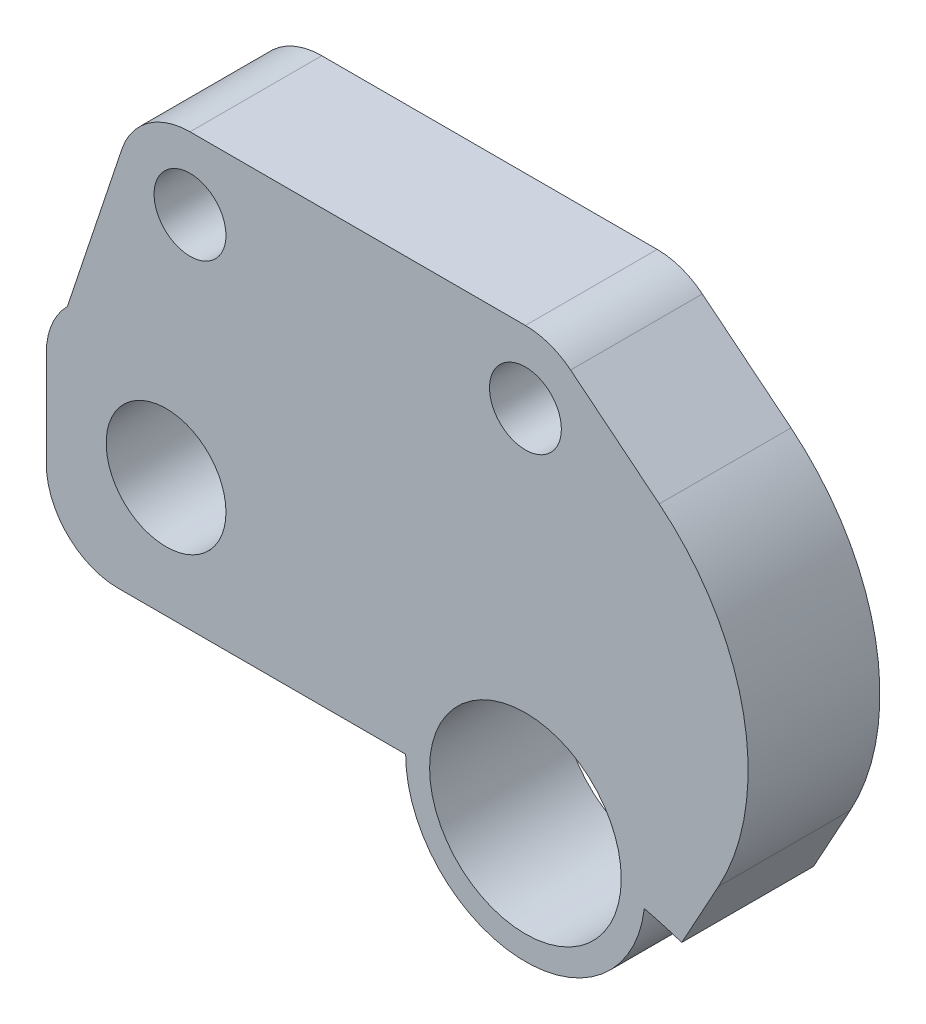
SolidWorks part; units mm, degrees
ref_plane "Alzado" through (0, 0, 0) normal (0, 0, 1) x (1, 0, 0)
ref_plane "Planta" through (0, 0, 0) normal (0, 1, 0) x (1, 0, 0)
ref_plane "Vista lateral" through (0, 0, 0) normal (1, 0, 0) x (0, 0, -1)
sketch "Croquis1" plane through (0, 0, 0) normal (0, 0, 1) x (1, 0, 0)
  line L0 (0, 0) -> (0, -20.95) construction
  line L1 (0, 0) -> (0, 20.95) construction
  line L2 (-20, 25.95) -> (-15, 25.95) construction
  line L3 (0, 20.95) -> (-4, 20.95)
  line L4 (0, 20.95) -> (0, 24.95)
  line L5 (0, 30.95) -> (-17, 30.95)
  line L6 (-20, 23.95) -> (-20, 27.95)
  line L7 (0, -25.95) -> (15.9531, -25.95)
  line L8 (-5, 20.95) -> (-17, 20.95)
  line L9 (0, 0) -> (18.3494, 18.3494) construction
  line L10 (0, 0) -> (25.95, 0) construction
  line L11 (-14, 30.95) -> (-14, 32.95) construction
  line L12 (0, 30.95) -> (0, 35.95) construction
  line L13 (0, 35.95) -> (-14, 35.95) construction
  line L14 (-16.8461, 36.8985) -> (-19.1213, 30.0713)
  line L15 (-14, 38.95) -> (0, 38.95)
  line L16 (1.8868, 38.2824) -> (19.4651, 24.0627)
  line L17 (-14, 34.45) -> (-14, 35.95) construction
  arc A0 (-3.9817, -20.5681) -> (3.9817, -20.5681) centre (0, 0) ccw
  arc A1 (17.6654, -25.4133) -> (0, 30.95) centre (0, 0) ccw
  arc A2 (-5, 20.95) -> (4.9643, 20.3533) centre (0, 20.95) ccw
  arc A3 (4.9643, -20.3533) -> (0, -25.95) centre (0, -20.95) ccw
  circle A4 centre (0, 20.95) radius 4
  circle A5 centre (0, -20.95) radius 4
  circle A6 centre (-15, 25.95) radius 2.5
  circle A7 centre (0, 0) radius 25.95 construction
  arc A8 (4.9643, -20.3533) -> (4.9643, 20.3533) centre (0, 0) ccw
  circle A9 centre (18.3494, 18.3494) radius 2
  circle A10 centre (25.95, 0) radius 2
  arc A11 (15.9531, -25.95) -> (17.6654, -25.4133) centre (15.9531, -22.95) ccw
  arc A12 (-17, 20.95) -> (-20, 23.95) centre (-17, 23.95) cw
  arc A13 (-17, 30.95) -> (-20, 27.95) centre (-17, 27.95) ccw
  circle A14 centre (-14, 35.95) radius 1.5
  circle A15 centre (0, 35.95) radius 1.5
  arc A16 (-14, 38.95) -> (-16.8461, 36.8985) centre (-14, 35.95) ccw
  arc A17 (1.8868, 38.2824) -> (0, 38.95) centre (0, 35.95) ccw
  arc A18 (13.1759, 16.288) -> (19.4651, 24.0627) centre (16.3205, 20.1753) ccw
  point P32 (-20, 30.95)
  dimension "D1" = 41.9
  dimension "D3" = 10
  dimension "D4" = 10
  dimension "D5" = 10
  dimension "D6" = 8
  dimension "D7" = 8
  dimension "D9" = 5
  dimension "D12" = 5
  dimension "D13" = 4
  dimension "D14" = 4
  dimension "D17" = 3
  dimension "D18" = 5
  dimension "D19" = 3
  dimension "D20" = 3
  dimension "D22" = 6
  dimension "D2" = 180
  dimension "D8" = 20
  dimension "D10" = 5
  dimension "D11" = 90
  dimension "D15" = 45
  dimension "D16" = 45
  dimension "D21" = 6
extrude "Saliente-Extruir1" add sketch "Croquis1" along normal blind 5.5 contours A8 A3 L7 A1 L5 L6 L8 A2 A6 A5 A4 | L16 A17 L15 A16 L14 A13 L5 A1 A14 A15 | A9
sketch "Croquis2" plane through (0, 0, 5.5) normal (0, 0, 1) x (1, 0, 0)
  line L0 (6.5263, 19.9075) -> (12.0871, 30.031)
  line L1 (1.8868, 38.2824) -> (19.4651, 24.0627) construction
  line L7 (19.4651, 24.0627) -> (1.8868, 38.2824)
  line L8 (0, 38.95) -> (-14, 38.95)
  line L9 (-16.8461, 36.8985) -> (-19.1213, 30.0713)
  line L10 (-20, 27.95) -> (-20, 23.95)
  line L11 (-17, 20.95) -> (-5, 20.95)
  line L12 (19.4651, 24.0627) -> (1.8868, 38.2824)
  line L13 (0, 38.95) -> (-14, 38.95)
  line L14 (-16.8461, 36.8985) -> (-19.1213, 30.0713)
  line L15 (-20, 27.95) -> (-20, 23.95)
  line L16 (-17, 20.95) -> (-5, 20.95)
  arc A0 (13.1759, 16.288) -> (4.9643, 20.3533) centre (0, 0) ccw construction
  arc A8 (13.1759, 16.288) -> (4.9643, 20.3533) centre (0, 0) ccw
  arc A9 (13.1759, 16.288) -> (19.4651, 24.0627) centre (16.3205, 20.1753) ccw
  arc A10 (1.8868, 38.2824) -> (0, 38.95) centre (0, 35.95) ccw
  arc A11 (-14, 38.95) -> (-16.8461, 36.8985) centre (-14, 35.95) ccw
  arc A12 (-19.1213, 30.0713) -> (-20, 27.95) centre (-17, 27.95) ccw
  arc A13 (-20, 23.95) -> (-17, 20.95) centre (-17, 23.95) ccw
  arc A14 (-5, 20.95) -> (4.9643, 20.3533) centre (0, 20.95) ccw
  arc A15 (13.1759, 16.288) -> (4.9643, 20.3533) centre (0, 0) ccw
  arc A16 (13.1759, 16.288) -> (19.4651, 24.0627) centre (16.3205, 20.1753) ccw
  arc A17 (1.8868, 38.2824) -> (0, 38.95) centre (0, 35.95) ccw
  arc A18 (-14, 38.95) -> (-16.8461, 36.8985) centre (-14, 35.95) ccw
  arc A19 (-19.1213, 30.0713) -> (-20, 27.95) centre (-17, 27.95) ccw
  arc A20 (-20, 23.95) -> (-17, 20.95) centre (-17, 23.95) ccw
  arc A21 (-5, 20.95) -> (4.9643, 20.3533) centre (0, 20.95) ccw
  arc M16 (4.9643, 20.3533) -> (13.1759, 16.288) centre (0, 0) cw
  arc M17 (13.1759, 16.288) -> (19.4651, 24.0627) centre (16.3205, 20.1753) ccw
  line M18 (19.4651, 24.0627) -> (1.8868, 38.2824)
  dimension "D1" = 0
extrude "Cortar-Extruir1" cut sketch "Croquis2" against normal blind 10 contours L0 M16 M17 M18
fillet "Redondeo1" radius 10 1 edges at (12.0871, 30.031, 2.75)
